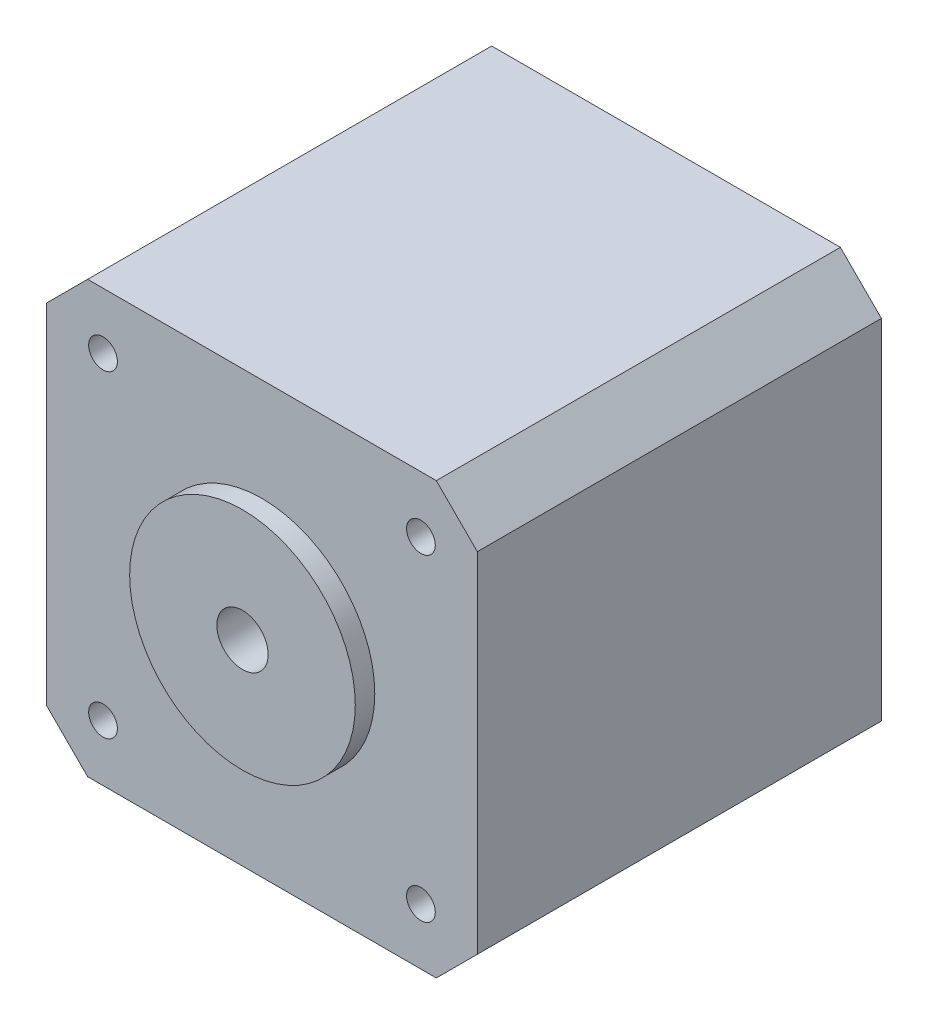
SolidWorks part; units mm, degrees
ref_plane "Alzado" through (0, 0, 0) normal (0, 0, 1) x (1, 0, 0)
ref_plane "Planta" through (0, 0, 0) normal (0, 1, 0) x (1, 0, 0)
ref_plane "Vista lateral" through (0, 0, 0) normal (1, 0, 0) x (0, 0, -1)
ref_plane "Plano1" through (0, 0, 0) normal (0, 0, -1) x (-1, 0, 0)
sketch "Croquis1" plane through (0, 0, 0) normal (0, 0, -1) x (-1, 0, 0)
  line L0 (0, 0) -> (0, 42)
  line L1 (0, 42) -> (-42, 42)
  line L2 (-42, 42) -> (-42, 0)
  line L3 (-42, 0) -> (0, 0)
extrude "Saliente-Extruir1" add sketch "Croquis1" against normal blind 39.4
sketch "Croquis2" plane through (0, 0, 0) normal (-1, 0, 0) x (0, 0, 1)
  line L0 (0, 29) -> (10.5, 29)
  line L1 (10.5, 29) -> (10.5, 13)
  line L2 (10.5, 13) -> (0, 13)
  line L3 (0, 13) -> (0, 29)
extrude "Saliente-Extruir2" add sketch "Croquis2" along normal blind 6.5
sketch "Croquis3" plane through (0, 0, 39.4) normal (0, 0, 1) x (1, 0, 0)
  circle A0 centre (21, 21) radius 11
extrude "Saliente-Extruir3" add sketch "Croquis3" along normal blind 1.9
sketch "Croquis4" plane through (0, 0, 41.3) normal (0, 0, 1) x (1, 0, 0)
  circle A0 centre (21, 21) radius 2.45
extrude "Saliente-Extruir4" add sketch "Croquis4" along normal blind 20.4
sketch "Croquis5" plane through (0, 0, 61.7) normal (0, 0, 1) x (1, 0, 0)
  line L0 (22.99, 22.4291) -> (22.99, 19.5709)
  arc A0 (22.99, 19.5709) -> (22.99, 22.4291) centre (21, 21) ccw
extrude "Cortar-Extruir1" cut sketch "Croquis5" against normal blind 15
hole_wizard "Diámetro de taladro Ø2.8 (2.8)1" positions "Croquis7" profile "Croquis6" hole size "Ø2.8" standard "Ansi Metric"
sketch "Croquis7" plane through (0, 0, 39.4) normal (0, 0, 1) x (1, 0, 0)
  point P0 (36.5, 5.5)
  point P1 (5.5, 5.5)
  point P2 (36.5, 36.5)
  point P3 (5.5, 36.5)
sketch "Croquis6" plane through (36.5, 5.5, 39.4) normal (1, 0, 0) x (0, -1, 0)
  line L0 (0, 0) -> (0, 3)
  line L1 (0, 3) -> (1.4, 3)
  line L2 (1.4, 3) -> (1.4, 0)
  line L5 (1.4, 0) -> (0, 0)
  line L10 (0, 3) -> (-1.4, 3) construction
  line L11 (0, -6.35) -> (0, 107.95) construction
  dimension "Diámetro de taladro" = 2.8
  dimension "Profundidad de taladro" = 3
  dimension "Ángulo de perforador" = 180
chamfer "Chaflán1" distance 4 angle 45 4 edges at (0, 0, 19.7) (42, 0, 19.7) (0, 42, 19.7) (42, 42, 19.7)
ref_plane "Plano2" through (0, 0, 61.7) normal (0, 0, 1) x (1, 0, 0)
sketch "Croquis8" plane through (0, 0, 61.7) normal (0, 0, 1) x (1, 0, 0)
  circle A0 centre (21, 21) radius 2.5
extrude "Cortar-Extruir2" cut sketch "Croquis8" against normal through all
